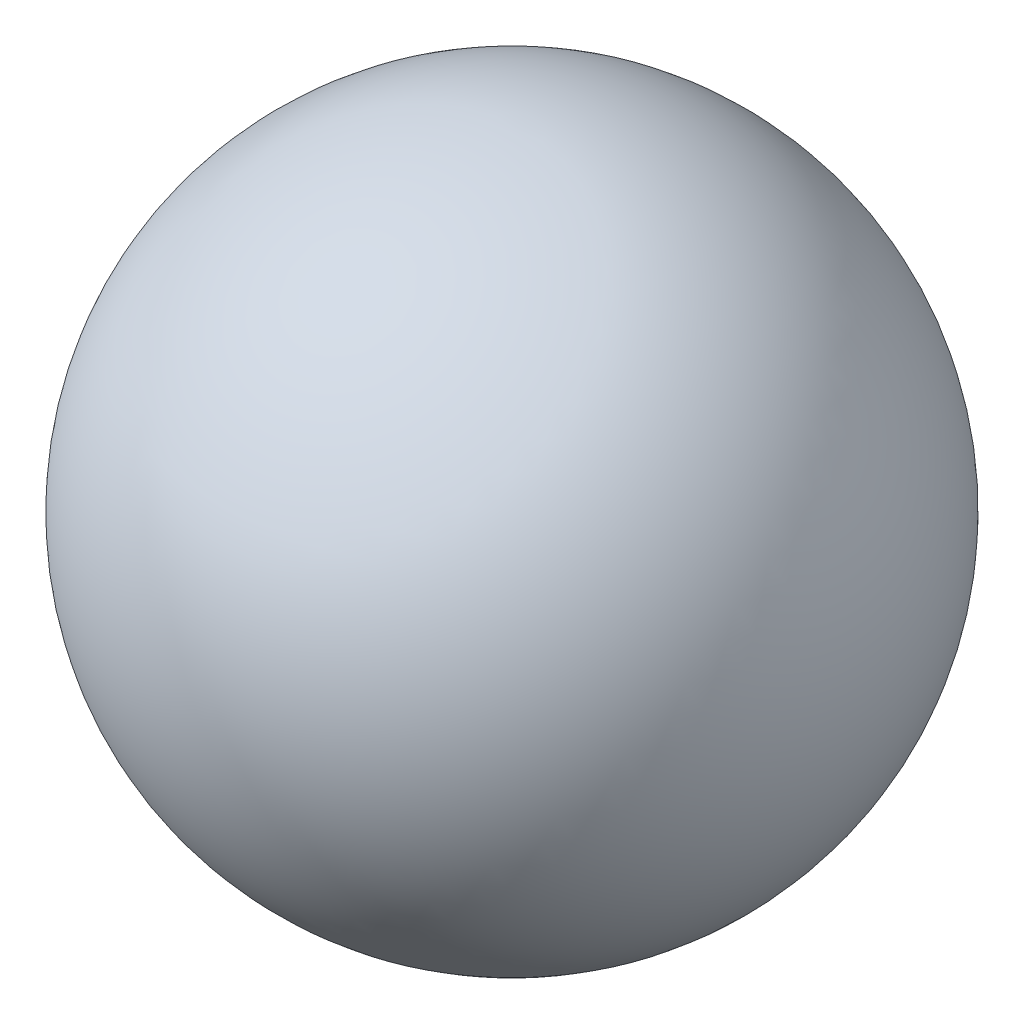
SolidWorks part; units mm, degrees
ref_plane "Front Plane" through (0, 0, 0) normal (0, 0, 1) x (1, 0, 0)
ref_plane "Top Plane" through (0, 0, 0) normal (0, 1, 0) x (1, 0, 0)
ref_plane "Right Plane" through (0, 0, 0) normal (1, 0, 0) x (0, 0, -1)
sketch "Sketch1" plane through (0, 0, 0) normal (0, 0, 1) x (1, 0, 0)
  line L0 (0, -26) -> (0, 30)
  line L1 (0, -26) -> (14.9666, -26)
  line L2 (30, 23.5212) -> (30, -40.8526) construction
  line L3 (0, 0) -> (0, 88.6378) construction
  arc A0 (0, 30) -> (14.9666, -26) centre (0, 0) cw
  dimension "D1" = 30
  dimension "D2" = 26
revolve "Revolve1" add sketch "Sketch1" angle 360 about L0
sketch "Sketch2" plane through (0, -26, 0) normal (0, -1, 0) x (1, 0, 0)
  circle A0 centre (0, 0) radius 6
  dimension "D1" = 12
extrude "Cut-Extrude1" cut sketch "Sketch2" against normal blind 12
